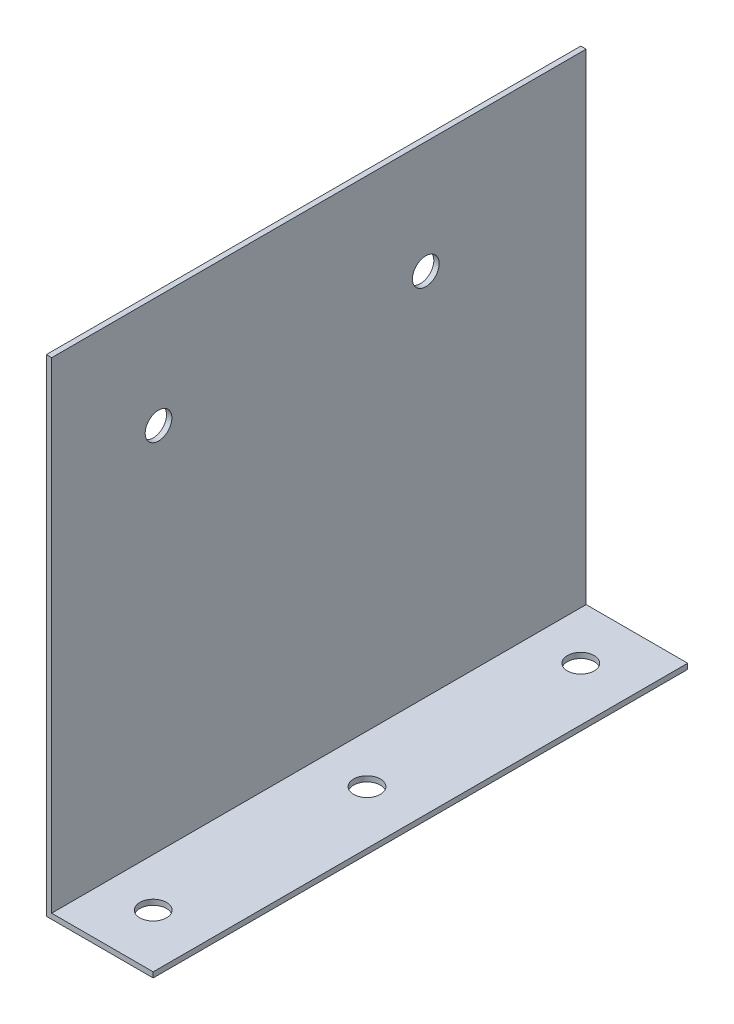
SolidWorks part; units mm, degrees
ref_plane "Piano frontale" through (0, 0, 0) normal (0, 0, 1) x (1, 0, 0)
ref_plane "Piano superiore" through (0, 0, 0) normal (0, 1, 0) x (1, 0, 0)
ref_plane "Piano destro" through (0, 0, 0) normal (1, 0, 0) x (0, 0, -1)
sketch "Schizzo1" plane through (0, 0, 0) normal (0, 1, 0) x (1, 0, 0)
  line L1 (0, 0) -> (20, 0)
  line L2 (0, 0) -> (0, -100)
  line L3 (0, -100) -> (20, -100)
  line L4 (20, 0) -> (20, -100)
  dimension "D1" = 20
  dimension "D2" = 100
extrude "Estrusione-Estrusione1" add sketch "Schizzo1" along normal blind 1
sketch "Schizzo2" plane through (0, 1, 0) normal (0, 1, 0) x (1, 0, 0)
  line L0 (0, -100) -> (20, -100) construction
  line L1 (0, 0) -> (1, 0)
  line L2 (0, 0) -> (0, -100)
  line L3 (0, -100) -> (1, -100)
  line L4 (1, 0) -> (1, -100)
  dimension "D1" = 1
extrude "Estrusione-Estrusione2" add sketch "Schizzo2" along normal blind 90 contours L2 L3 L4 L1
sketch "Schizzo3" plane through (0, 1, 0) normal (0, 1, 0) x (1, 0, 0)
  line L0 (1, -100) -> (20, -100) construction
  line L1 (20, 0) -> (1, 0) construction
  line L2 (20, -100) -> (20, 0) construction
  circle A0 centre (10, -90) radius 2.5
  circle A1 centre (10, -50) radius 2.5
  circle A2 centre (10, -10) radius 2.5
  dimension "D1" = 5
  dimension "D2" = 5
  dimension "D3" = 5
  dimension "D4" = 10
  dimension "D5" = 10
  dimension "D6" = 50
  dimension "D7" = 10
  dimension "D8" = 10
  dimension "D9" = 10
extrude "Taglio-Estrusione1" cut sketch "Schizzo3" against normal blind 42
sketch "Schizzo4" plane through (1, 0, 0) normal (1, 0, 0) x (0, 0, -1)
  line L0 (0, 91) -> (0, 1) construction
  line L1 (0, 91) -> (-100, 91) construction
  circle A0 centre (-30, 70) radius 2.5
  circle A1 centre (-80, 70) radius 2.5
  dimension "D1" = 5
  dimension "D2" = 5
  dimension "D3" = 30
  dimension "D4" = 50
  dimension "D5" = 21
  dimension "D6" = 21
extrude "Taglio-Estrusione2" cut sketch "Schizzo4" against normal blind 42
